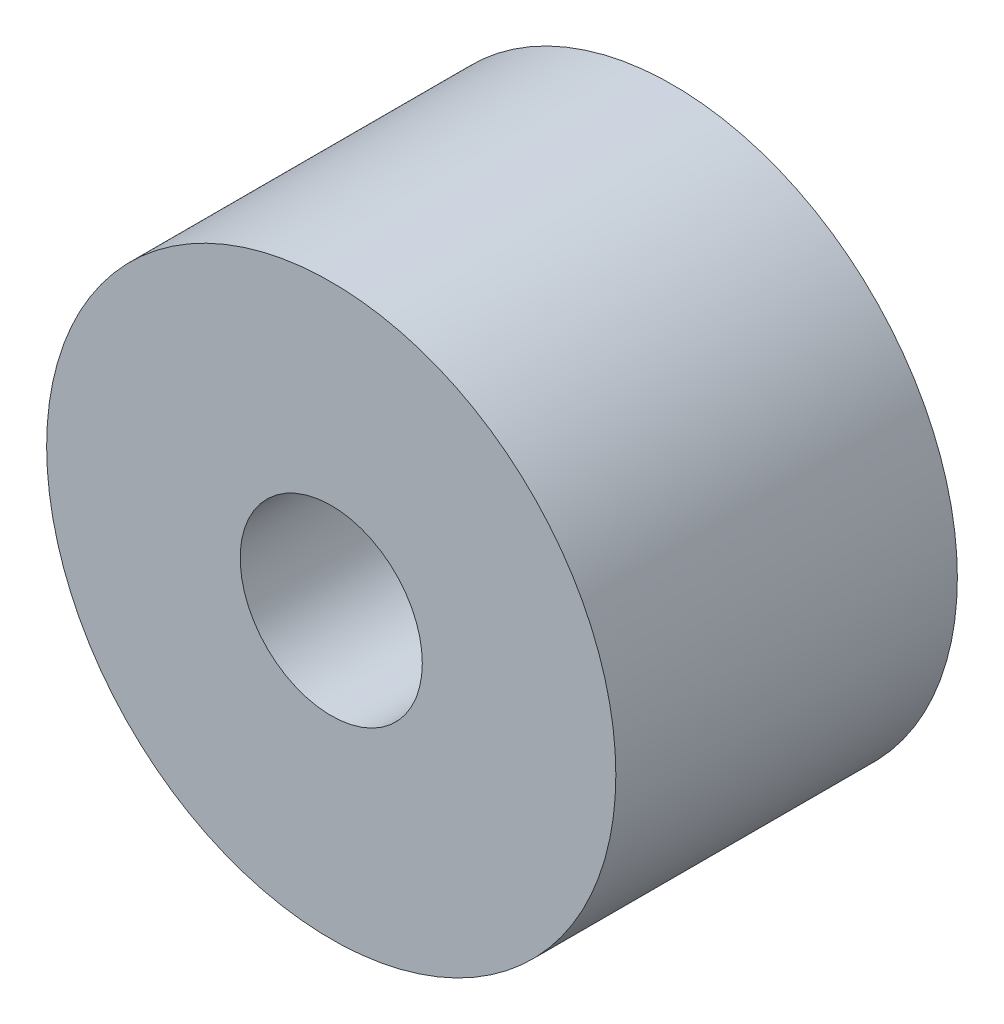
SolidWorks part; units mm, degrees
ref_plane "Front Plane" through (0, 0, 0) normal (0, 0, 1) x (1, 0, 0)
ref_plane "Top Plane" through (0, 0, 0) normal (0, 1, 0) x (1, 0, 0)
ref_plane "Right Plane" through (0, 0, 0) normal (1, 0, 0) x (0, 0, -1)
sketch "Sketch1" plane through (0, 0, 0) normal (0, 0, 1) x (1, 0, 0)
  circle A0 centre (0, 0) radius 12.5
  circle A1 centre (0, 0) radius 4
  dimension "D1" = 8
  dimension "D2" = 25
extrude "Boss-Extrude2" add sketch "Sketch1" along normal blind 15
